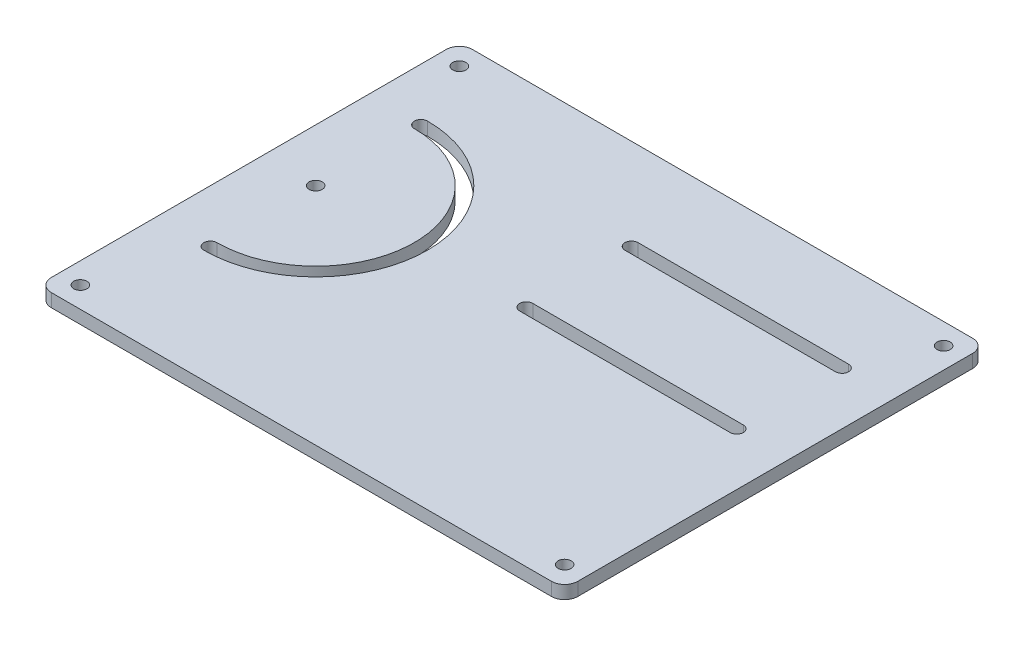
SolidWorks part; units mm, degrees
ref_plane "Front Plane" through (0, 0, 0) normal (0, 0, 1) x (1, 0, 0)
ref_plane "Top Plane" through (0, 0, 0) normal (0, 1, 0) x (1, 0, 0)
ref_plane "Right Plane" through (0, 0, 0) normal (1, 0, 0) x (0, 0, -1)
sketch "Sketch1" plane through (0, 0, 0) normal (0, 1, 0) x (1, 0, 0)
  line L0 (12.7, 81.2166) -> (12.7, 70.1339) construction
  line L1 (3.175, 0) -> (123.825, 0)
  line L2 (0, 3.175) -> (0, 98.425)
  line L3 (3.175, 101.6) -> (123.825, 101.6)
  line L4 (127, 3.175) -> (127, 98.425)
  line L5 (63.5, 81.2166) -> (114.3, 81.2166)
  line L6 (63.5, 78.0416) -> (114.3, 78.0416)
  line L7 (-29.7008, 44.6071) -> (59.2279, 44.6071) construction
  line L8 (63.5, 79.6291) -> (114.3, 79.6291) construction
  line L9 (9.8429, 66.9291) -> (17.6906, 66.9291) construction
  line L10 (63.5, 55.8166) -> (114.3, 55.8166)
  line L11 (63.5, 52.6416) -> (114.3, 52.6416)
  arc A0 (12.7, 78.0416) -> (12.7, 30.4166) centre (12.7, 54.2291) cw
  circle A1 centre (12.7, 54.2291) radius 1.5875
  arc A2 (12.7, 81.2166) -> (12.7, 27.2416) centre (12.7, 54.2291) cw
  arc A3 (12.7, 81.2166) -> (12.7, 78.0416) centre (12.7, 79.6291) ccw
  arc A4 (12.7, 27.2416) -> (12.7, 30.4166) centre (12.7, 28.8291) cw
  arc A5 (63.5, 78.0416) -> (63.5, 81.2166) centre (63.5, 79.6291) cw
  arc A6 (114.3, 78.0416) -> (114.3, 81.2166) centre (114.3, 79.6291) ccw
  arc A7 (114.3, 55.8166) -> (114.3, 52.6416) centre (114.3, 54.2291) cw
  arc A8 (63.5, 55.8166) -> (63.5, 52.6416) centre (63.5, 54.2291) ccw
  circle A9 centre (5.08, 96.52) radius 1.5875
  circle A10 centre (5.08, 5.08) radius 1.5875
  arc A11 (12.7, 79.6291) -> (12.7, 28.8291) centre (12.7, 54.2291) cw construction
  circle A12 centre (121.92, 96.52) radius 1.5875
  circle A13 centre (121.92, 5.08) radius 1.5875
  arc A14 (0, 3.175) -> (3.175, 0) centre (3.175, 3.175) ccw
  arc A15 (123.825, 0) -> (127, 3.175) centre (123.825, 3.175) ccw
  arc A16 (127, 98.425) -> (123.825, 101.6) centre (123.825, 98.425) ccw
  arc A17 (3.175, 101.6) -> (0, 98.425) centre (3.175, 98.425) ccw
  point P44 (0, 0)
  point P49 (127, 101.6)
  point P52 (0, 101.6)
  dimension "D2" = 3.175
  dimension "D3" = 25.4
  dimension "D4" = 3.175
  dimension "D5" = 3.175
  dimension "D10" = 3.175
  dimension "D15" = 3.175
  dimension "D16" = 3.175
  dimension "D17" = 5.08
  dimension "D21" = 3.175
  dimension "D23" = 20.3834
  dimension "D25" = 12.7
  dimension "D26" = 3.175
  dimension "D1" = 101.6
  dimension "10" = 127
  dimension "D7" = 12.7
  dimension "D8" = 12.7
  dimension "D9" = 12.7
  dimension "D11" = 5.08
  dimension "D12" = 5.08
  dimension "D13" = 5.08
  dimension "D14" = 5.08
  dimension "D18" = 5.08
  dimension "D19" = 5.08
  dimension "D20" = 5.08
  dimension "D22" = 50.8
  dimension "D6" = 1.5875
extrude "Boss-Extrude1" add sketch "Sketch1" along normal blind 3.175 contours L1 L4 L3 L2 A13 A12 A10 A9 A8 L10 A7 L11 A6 L6 A5 L5 A1 A2 A4 A0 A3
